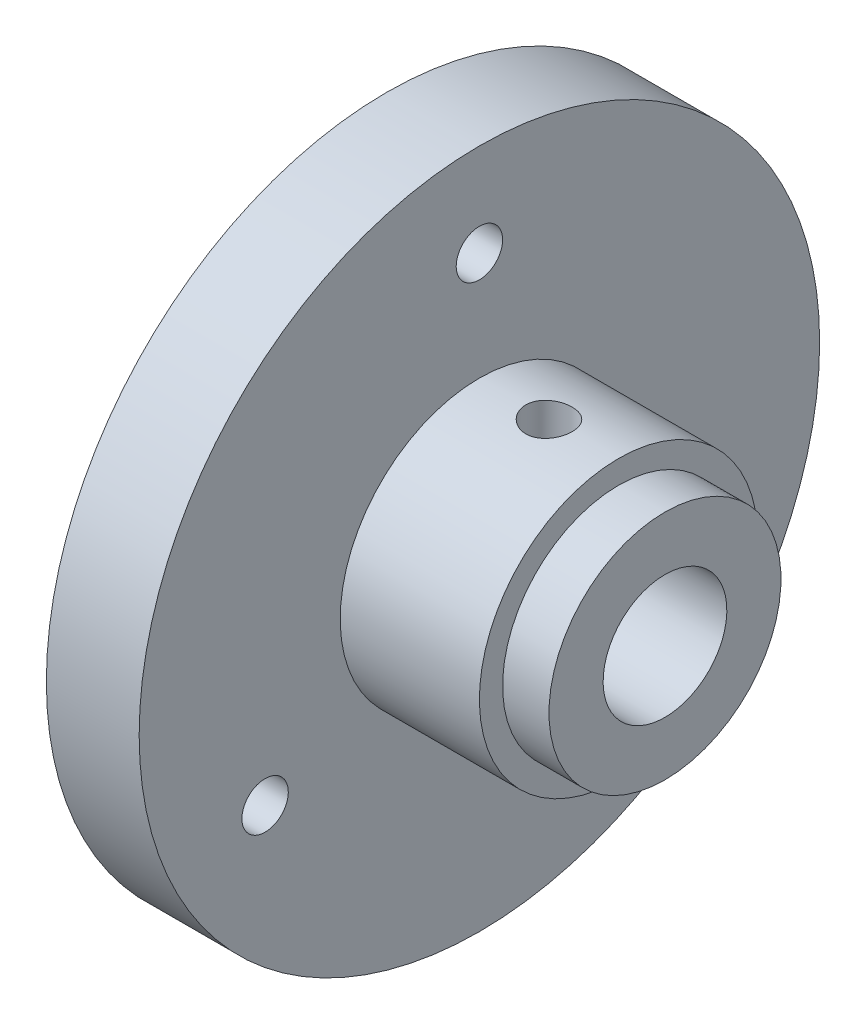
SolidWorks part; units mm, degrees
ref_plane "Plan de face" through (0, 0, 0) normal (0, 0, 1) x (1, 0, 0)
ref_plane "Plan de dessus" through (0, 0, 0) normal (0, 1, 0) x (1, 0, 0)
ref_plane "Plan de droite" through (0, 0, 0) normal (1, 0, 0) x (0, 0, -1)
sketch "Esquisse1" plane through (0, 0, 0) normal (0, 0, 1) x (1, 0, 0)
  line L0 (0, 0) -> (-18, 0) construction
  line L1 (0, 4) -> (-18, 4)
  line L3 (-3, 9) -> (-12, 9)
  line L7 (-12, 22) -> (-18, 22)
  line L8 (-18, 4) -> (-18, 22)
  line L9 (-18, 4) -> (-18, 0) construction
  line L10 (-3, 9) -> (-3, 7.5)
  line L11 (-12, 22) -> (-12, 9)
  line L14 (-3, 7.5) -> (0, 7.5)
  line L15 (0, 4) -> (0, 7.5)
  line L16 (0, 4) -> (0, 0) construction
  dimension "D1" = 4
  dimension "D2" = 22
  dimension "D3" = 6
  dimension "D4" = 9
  dimension "D5" = 9
  dimension "D6" = 7.5
  dimension "D7" = 3
revolve "Révolution1" add sketch "Esquisse1" angle 360 about L0
sketch "Esquisse2" plane through (-12, 0, 0) normal (1, 0, 0) x (0, 0, -1)
  line L0 (0, 16) -> (0, 0) construction
  circle A0 centre (0, 16) radius 1.5
  circle A1 centre (13.8564, -8) radius 1.5
  circle A2 centre (-13.8564, -8) radius 1.5
  point P11 (0, 0)
  dimension "D1" = 3
  dimension "D2" = 16
  dimension "D3" = 3
extrude "Enlèv. mat.-Extru.1" cut sketch "Esquisse2" against normal through all
ref_plane "Plan2" through (0, 9, 0) normal (0, 1, 0) x (1, 0, 0)
sketch "Esquisse3" plane through (0, 9, 0) normal (0, 1, 0) x (1, 0, 0)
  line L0 (-3, 0) -> (-12, 0) construction
  line L1 (-12, -1.5) -> (-12, 1.5) construction
  line L2 (-3, -7.5) -> (-3, 7.5) construction
  circle A0 centre (-7.5, 0) radius 1.5
  point P8 (-7.5, 0)
  dimension "D1" = 3
extrude "Enlèv. mat.-Extru.2" cut sketch "Esquisse3" against normal up to next
